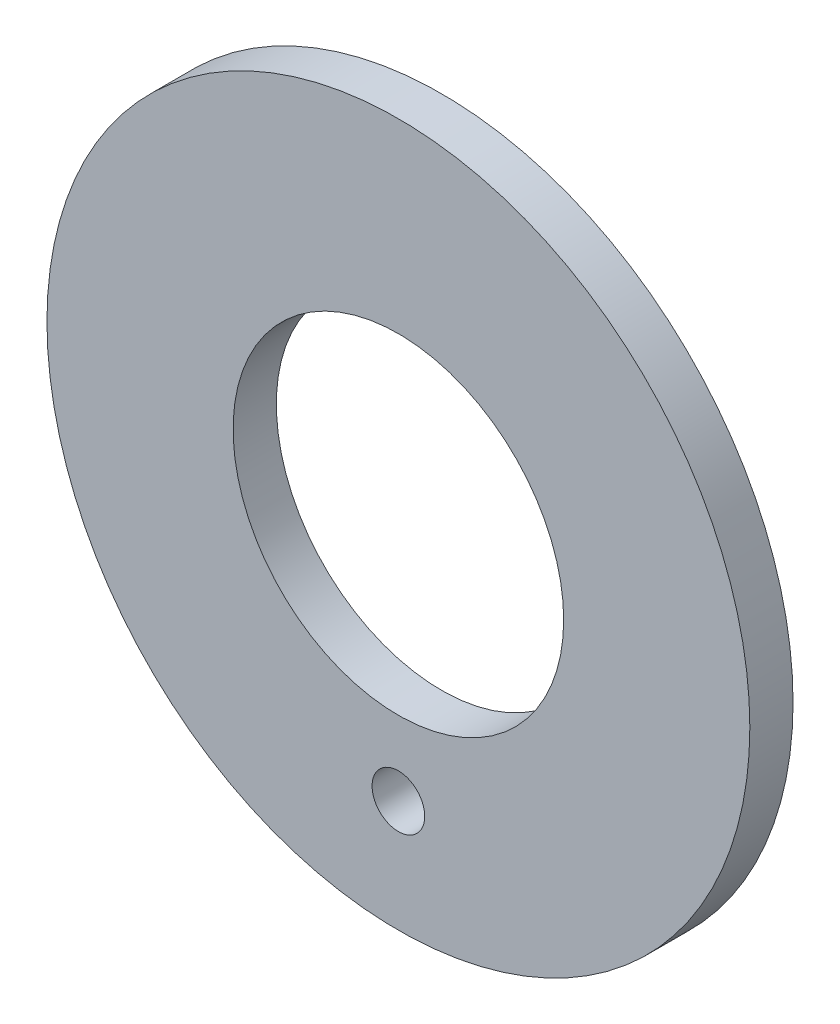
SolidWorks part; units mm, degrees
ref_plane "Front Plane" through (0, 0, 0) normal (0, 0, 1) x (1, 0, 0)
ref_plane "Top Plane" through (0, 0, 0) normal (0, 1, 0) x (1, 0, 0)
ref_plane "Right Plane" through (0, 0, 0) normal (1, 0, 0) x (0, 0, -1)
sketch "Sketch1" plane through (0, 0, 0) normal (0, 0, 1) x (1, 0, 0)
  circle A0 centre (0, 0) radius 11.176
  circle A1 centre (0, -7.62) radius 0.762 construction
  circle A2 centre (0, -7.62) radius 0.837
  circle A3 centre (0, 0) radius 5.1562 construction
  circle A4 centre (0, 0) radius 5.2562
  dimension "D1" = 22.352
  dimension "D2" = 1.524
  dimension "D4" = 0.075
  dimension "D5" = 10.3124
  dimension "D6" = 0.1
  dimension "D3" = 7.62
extrude "Boss-Extrude1" add sketch "Sketch1" along normal blind 1.374
